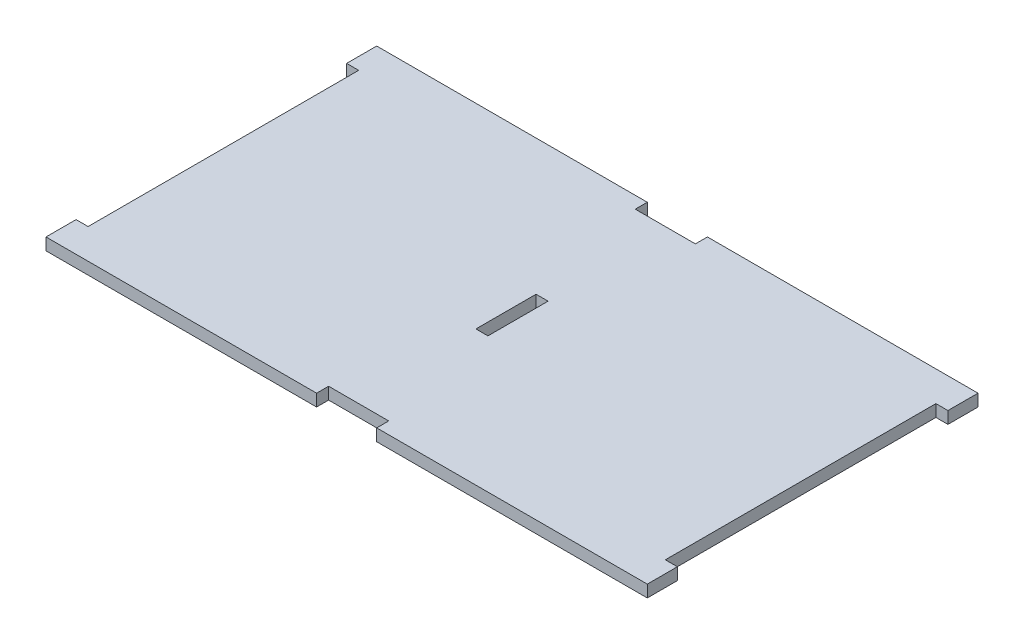
SolidWorks part; units mm, degrees
ref_plane "Front Plane" through (0, 0, 0) normal (0, 0, 1) x (1, 0, 0)
ref_plane "Top Plane" through (0, 0, 0) normal (0, 1, 0) x (1, 0, 0)
ref_plane "Right Plane" through (0, 0, 0) normal (1, 0, 0) x (0, 0, -1)
sketch "Sketch1" plane through (0, 0, 0) normal (0, 1, 0) x (1, 0, 0)
  line L0 (-50, 27.5) -> (50, -27.5) construction
  line L5 (50, 27.5) -> (-50, -27.5) construction
  line L6 (-50, 22.5) -> (-48, 22.5)
  line L7 (-48, 22.5) -> (-48, -22.5)
  line L8 (-48, -22.5) -> (-50, -22.5)
  line L9 (-50, 27.5) -> (-50, 22.5)
  line L10 (-50, -22.5) -> (-50, -27.5)
  line L11 (50, 27.5) -> (50, 22.5)
  line L12 (50, 22.5) -> (48, 22.5)
  line L13 (48, 22.5) -> (48, -22.5)
  line L14 (48, -22.5) -> (50, -22.5)
  line L15 (50, -22.5) -> (50, -27.5)
  line L16 (-50, 27.5) -> (-5, 27.5)
  line L17 (-5, 27.5) -> (-5, 25.5)
  line L18 (-5, 25.5) -> (5, 25.5)
  line L19 (5, 25.5) -> (5, 27.5)
  line L20 (5, 27.5) -> (50, 27.5)
  line L21 (-50, -27.5) -> (-5, -27.5)
  line L22 (-5, -27.5) -> (-5, -25.5)
  line L23 (-5, -25.5) -> (5, -25.5)
  line L24 (5, -25.5) -> (5, -27.5)
  line L25 (5, -27.5) -> (50, -27.5)
  line L26 (-1, -5) -> (1, 5) construction
  line L27 (-1, 5) -> (1, 5)
  line L28 (-1, 5) -> (-1, -5)
  line L29 (-1, -5) -> (1, -5)
  line L30 (1, 5) -> (1, -5)
  line L31 (-1, 5) -> (1, -5) construction
  circle A0 centre (0, 0) radius 7.5 construction
  dimension "D3" = 15
  dimension "D1" = 100
  dimension "D2" = 55
  dimension "D4" = 2
  dimension "D5" = 5
  dimension "D6" = 10
  dimension "D7" = 2
  dimension "D8" = 10
extrude "Boss-Extrude1" add sketch "Sketch1" along normal blind 2
